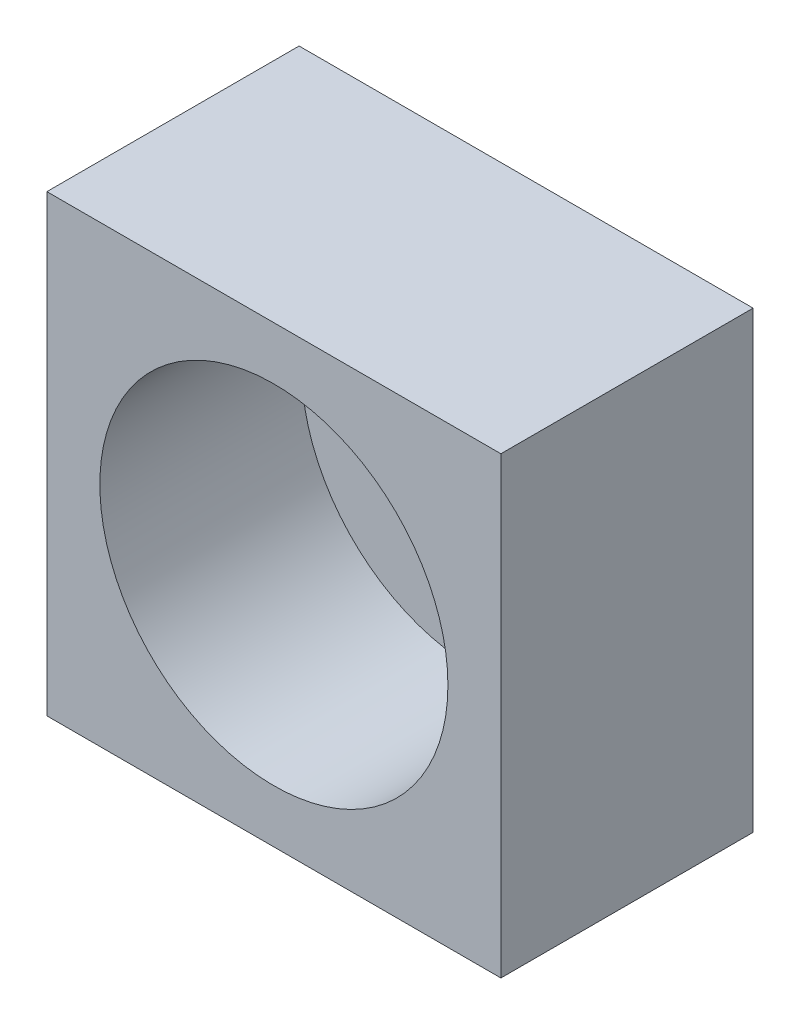
SolidWorks part; units mm, degrees
ref_plane "Alzado" through (0, 0, 0) normal (0, 0, 1) x (1, 0, 0)
ref_plane "Planta" through (0, 0, 0) normal (0, 1, 0) x (1, 0, 0)
ref_plane "Vista lateral" through (0, 0, 0) normal (1, 0, 0) x (0, 0, -1)
sketch "Croquis1" plane through (0, 0, 0) normal (0, 0, 1) x (1, 0, 0)
  line L1 (-9, -9) -> (9, -9)
  line L2 (-9, -9) -> (-9, 9)
  line L3 (-9, 9) -> (9, 9)
  line L4 (9, -9) -> (9, 9)
  line L5 (-9, -9) -> (9, 9) construction
  line L6 (-9, 9) -> (9, -9) construction
  point P0 (0, 0)
  dimension "D1" = 18
  dimension "D2" = 18
extrude "Saliente-Extruir1" add sketch "Croquis1" along normal blind 10
sketch "Croquis2" plane through (0, 0, 10) normal (0, 0, 1) x (1, 0, 0)
  circle A0 centre (0, 0) radius 6.9
  dimension "D1" = 13.8
extrude "Cortar-Extruir1" cut sketch "Croquis2" against normal blind 8
sketch "Croquis3" plane through (0, 0, 2) normal (0, 0, 1) x (1, 0, 0)
  circle A0 centre (0, 0) radius 2.75
  dimension "D1" = 5.5
extrude "Cortar-Extruir2" cut sketch "Croquis3" against normal blind 8
